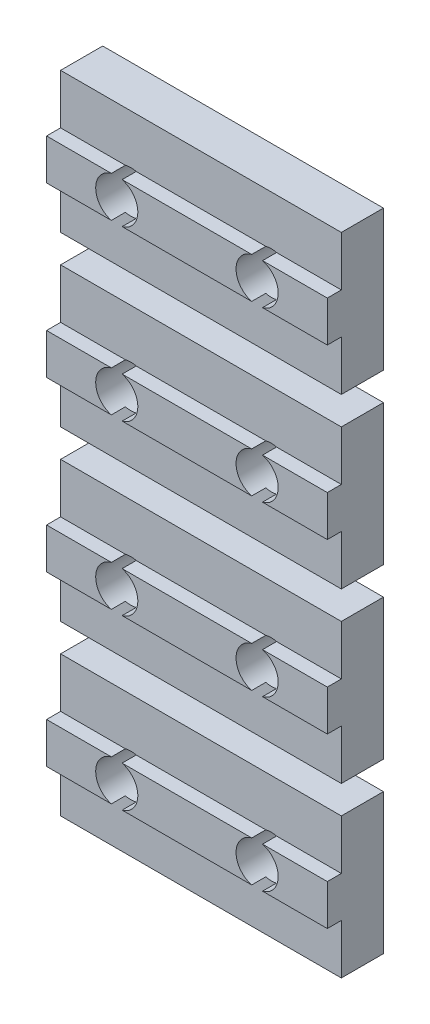
SolidWorks part; units mm, degrees
ref_plane "Front Plane" through (0, 0, 0) normal (0, 0, 1) x (1, 0, 0)
ref_plane "Top Plane" through (0, 0, 0) normal (0, 1, 0) x (1, 0, 0)
ref_plane "Right Plane" through (0, 0, 0) normal (1, 0, 0) x (0, 0, -1)
sketch "Esquisse1" plane through (0, 0, 0) normal (0, 0, 1) x (1, 0, 0)
  line L1 (0, 0) -> (20, 0)
  line L2 (0, 0) -> (0, 10)
  line L3 (0, 10) -> (20, 10)
  line L4 (20, 0) -> (20, 10)
  dimension "D1" = 20
  dimension "D2" = 10
extrude "Main" add sketch "Esquisse1" along normal blind 3
sketch "Esquisse2" plane through (0, 0, 3) normal (0, 0, 1) x (1, 0, 0)
  line L0 (20, 0) -> (20, 10) construction
  line L1 (20, 3.55) -> (0, 3.55)
  line L2 (20, 3.55) -> (20, 6.45)
  line L3 (20, 6.45) -> (0, 6.45)
  line L4 (0, 3.55) -> (0, 6.45)
  line L5 (0, 10) -> (0, 0) construction
  line L6 (0, 10) -> (0, 0) construction
  point P8 (0, 5)
  point P9 (0, 5)
  dimension "D1" = 2.9
extrude "CentralFix" add sketch "Esquisse2" along normal blind 1
sketch "Esquisse3" plane through (0, 0, 0) normal (0, 0, -1) x (-1, 0, 0)
  line L0 (-20, 0) -> (-20, 10) construction
  line L1 (0, 6.45) -> (0, 3.55) construction
  circle A0 centre (-15, 5) radius 1.5
  circle A1 centre (-5, 5) radius 1.5
  point P5 (-20, 5)
  point P9 (0, 0)
  dimension "D1" = 3
  dimension "D2" = 5
  dimension "D3" = 5
extrude "HolesFix" cut sketch "Esquisse3" against normal through all
pattern_linear "LPattern1" count 4 spacing 12 along (0, 1, 0) of "Main"
